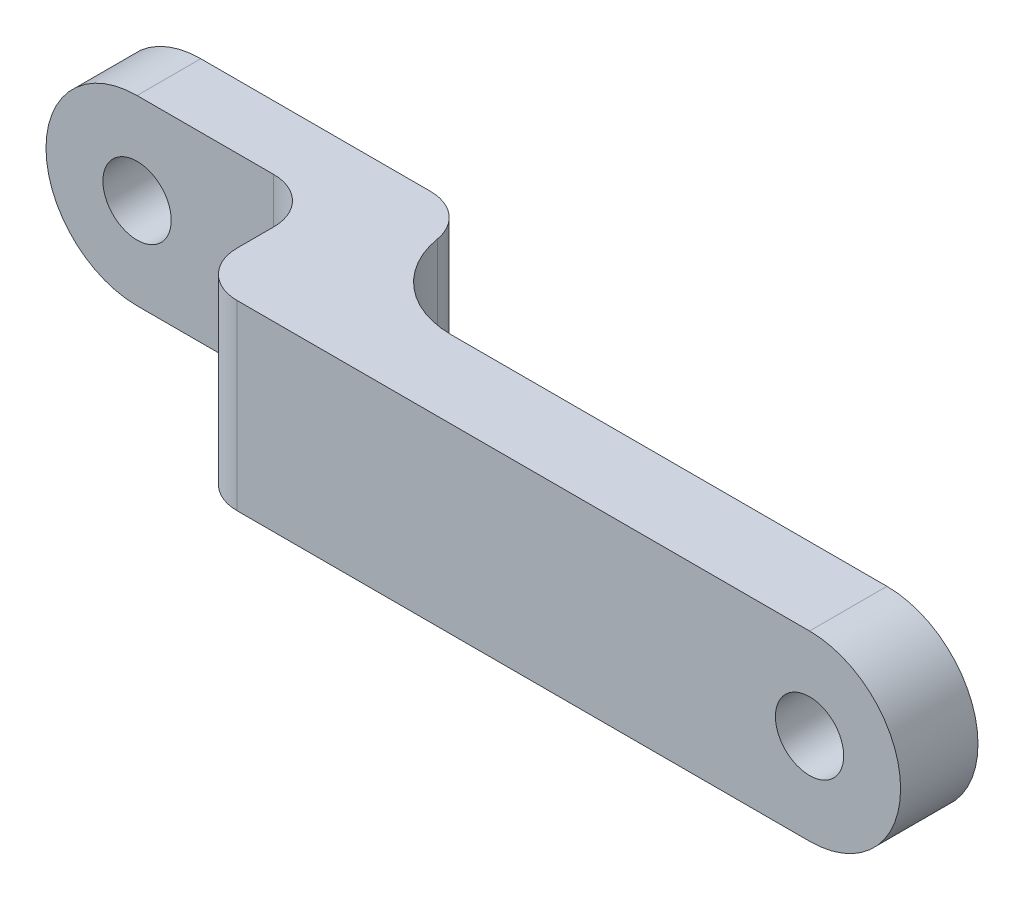
SolidWorks part; units mm, degrees
ref_plane "Front" through (0, 0, 0) normal (0, 0, 1) x (1, 0, 0)
ref_plane "Top" through (0, 0, 0) normal (0, 1, 0) x (1, 0, 0)
ref_plane "Right" through (0, 0, 0) normal (1, 0, 0) x (0, 0, -1)
sketch "Sketch1" plane through (0, 0, 0) normal (0, 0, 1) x (1, 0, 0)
  line L0 (0, 0) -> (17.57, 0) construction
  line L1 (0, 2) -> (17.57, 2)
  line L2 (0, -2) -> (17.57, -2)
  circle A0 centre (0, 0) radius 0.75
  circle A1 centre (17.57, 0) radius 0.75
  arc A2 (0, 2) -> (0, -2) centre (0, 0) ccw
  arc A3 (17.57, -2) -> (17.57, 2) centre (17.57, 0) ccw
  point P5 (8.785, 0)
  dimension "D1" = 1.5
  dimension "D3" = 2
  dimension "D2" = 17.57
extrude "Boss-Extrude1" add sketch "Sketch1" along normal mid plane 1.7
sketch "Sketch2" plane through (0, 0, -0.85) normal (0, 0, -1) x (-1, 0, 0)
  line L0 (-6, 2) -> (-6, -2)
  line L2 (0, 2) -> (-17.57, 2)
  line L3 (-17.57, -2) -> (0, -2)
  line L4 (0, 2) -> (-6, 2)
  line L5 (-6, -2) -> (0, -2)
  circle A0 centre (0, 0) radius 0.75 construction
  circle A1 centre (0, 0) radius 0.75
  arc A2 (0, -2) -> (0, 2) centre (0, 0) ccw
  arc A3 (-17.57, 2) -> (-17.57, -2) centre (-17.57, 0) ccw
  arc A4 (0, -2) -> (0, 2) centre (0, 0) ccw
  dimension "D2" = 6
  dimension "D1" = 0
extrude "Boss-Extrude2" add sketch "Sketch2" along normal blind 2.5 contours L4 L0 L5 A4
sketch "Sketch3" plane through (0, 0, 0.85) normal (0, 0, 1) x (1, 0, 0)
  line L0 (4, 2) -> (4, -2)
  line L1 (6, 2) -> (6, -2) construction
  line L2 (0, -2) -> (17.57, -2)
  line L3 (17.57, 2) -> (0, 2)
  line L4 (0, -2) -> (4, -2)
  line L5 (4, 2) -> (0, 2)
  circle A0 centre (0, 0) radius 0.75 construction
  circle A1 centre (0, 0) radius 0.75
  arc A2 (0, 2) -> (0, -2) centre (0, 0) ccw
  arc A3 (17.57, -2) -> (17.57, 2) centre (17.57, 0) ccw
  arc A4 (0, 2) -> (0, -2) centre (0, 0) ccw
  dimension "D2" = 2
  dimension "D1" = 0
extrude "Cut-Extrude1" cut sketch "Sketch3" against normal blind 2.8
fillet "Fillet1" radius 2 1 edges at (6, 0, -0.85)
fillet "Fillet2" radius 1 1 edges at (6, 0, -3.35)
fillet "Fillet3" radius 1 2 edges at (4, 0, -1.95) (4, 0, 0.85)
